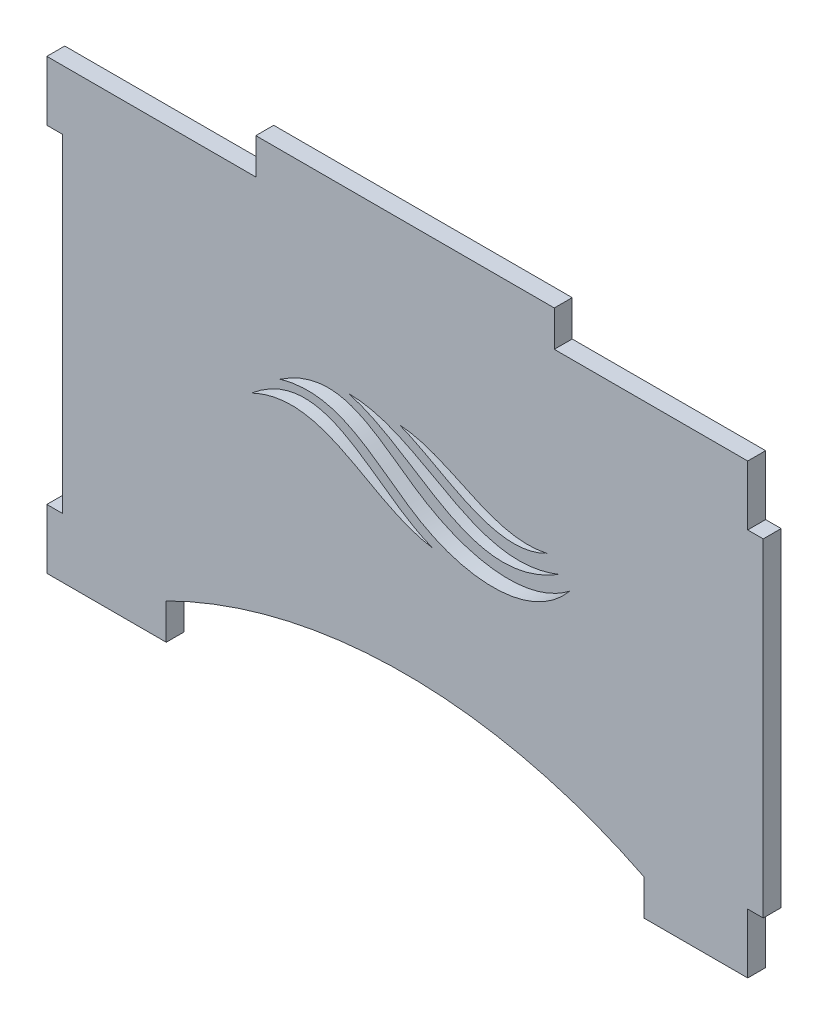
SolidWorks part; units mm, degrees
ref_plane "Front Plane" through (0, 0, 0) normal (0, 0, 1) x (1, 0, 0)
ref_plane "Top Plane" through (0, 0, 0) normal (0, 1, 0) x (1, 0, 0)
ref_plane "Right Plane" through (0, 0, 0) normal (1, 0, 0) x (0, 0, -1)
sketch "Sketch1" plane through (0, 0, 0) normal (0, 0, 1) x (1, 0, 0)
  line L0 (-58.7, -75) -> (-38.7, -75)
  line L3 (-58.7, 0) -> (58.7, 0) construction
  line L5 (58.7, 0) -> (58.7, -10)
  line L6 (58.7, -10) -> (61.3, -10)
  line L7 (58.7, -75) -> (41.3, -75)
  line L8 (61.3, -10) -> (61.3, -65)
  line L9 (61.3, -65) -> (58.7, -65)
  line L10 (58.7, -65) -> (58.7, -75)
  line L11 (-58.7, -75) -> (-58.7, -65)
  line L12 (-58.7, -65) -> (-56.1, -65)
  line L13 (-56.1, -65) -> (-56.1, -10)
  line L14 (-56.1, -10) -> (-58.7, -10)
  line L15 (-58.7, -10) -> (-58.7, 0)
  line L16 (-23.7, 6) -> (26.3, 6)
  line L17 (26.3, 6) -> (26.3, 0)
  line L18 (26.3, 0) -> (58.7, 0)
  line L19 (-23.7, 6) -> (-23.7, 0)
  line L20 (-23.7, 0) -> (-58.7, 0)
  line L21 (41.3, -75) -> (41.3, -69)
  line L22 (41.3, -69) -> (-38.7, -69)
  line L23 (-38.7, -69) -> (-38.7, -75)
  point P0 (0, 0)
  dimension "D1" = 20
  dimension "D3" = 2.6
  dimension "D2" = 120
  dimension "D4" = 20
  dimension "D5" = 6
  dimension "D6" = 50
  dimension "D7" = 10
  dimension "D8" = 75
  dimension "D9" = 6
extrude "Boss-Extrude1" add sketch "Sketch1" along normal blind 3 contours L7 L21 L22 L23 L0 L11 L12 L13 L14 L15 L20 L19 L16 L17 L18 L5 L6 L8 L9 L10
sketch "Sketch2" plane through (0, 0, 0) normal (0, 0, -1) x (-1, 0, 0)
  spline S0 degree 3 poles (24.4334, -31.7116) (12.0869, -21.3752) (4.1402, -35.3582) (-5.9728, -39.0225) knots 0 0 0 0 1 1 1 1
  spline S1 degree 3 poles (24.4334, -31.7116) (12.2668, -25.8916) (4.7867, -37.5421) (-5.9728, -39.0225) knots 0 0 0 0 1 1 1 1
  spline S2 degree 3 poles (19.6339, -27.3096) (8.7369, -24.1379) (-2.1411, -40.4781) (-22.7929, -41.1922) (-28.8934, -33.7725) knots 0 0 0 0 0.516039 1 1 1 1
  spline S3 degree 3 poles (19.6339, -27.3096) (9.0234, -20.1868) (-2.4042, -35.7492) (-21.9217, -39.1582) (-28.8934, -33.7725) knots 0 0 0 0 0.521405 1 1 1 1
  spline S4 degree 3 poles (8.1698, -23.626) (-3.7885, -26.9187) (-12.4208, -41.2866) (-27.1251, -32.2465) knots 0 0 0 0 1 1 1 1
  spline S5 degree 3 poles (8.1698, -23.626) (-4.8002, -23.7533) (-12.7202, -38.0151) (-27.1251, -32.2465) knots 0 0 0 0 1 1 1 1
  spline S6 degree 3 poles (-0.3748, -23.9123) (-7.802, -26.7598) (-16.4033, -34.7893) (-25.1259, -30.1784) knots 0 0 0 0 1 1 1 1
  spline S7 degree 3 poles (-0.3748, -23.9123) (-9.1802, -24.4868) (-15.7739, -32.3988) (-25.1259, -30.1784) knots 0 0 0 0 1 1 1 1
extrude "Cut-Extrude1" cut sketch "Sketch2" against normal through all
sketch "Sketch3" [suppressed] plane through (0, 0, 0) normal (0, 0, -1) x (-1, 0, 0)
  line L0 (23.7, 6) -> (-26.3, 6) construction
  line L1 (-24.8, 6) -> (-27.8, 6)
  line L2 (-24.8, 6) -> (-24.8, -30)
  line L3 (-24.8, -30) -> (-27.8, -30)
  line L4 (-27.8, 6) -> (-27.8, -30)
  line L5 (-26.3, 0) -> (-58.7, 0) construction
  line L6 (22.2, 6) -> (25.2, 6)
  line L7 (22.2, 6) -> (22.2, -30)
  line L8 (22.2, -30) -> (25.2, -30)
  line L9 (25.2, 6) -> (25.2, -30)
  line L10 (-26.3, 6) -> (-26.3, 0) construction
  line L11 (23.7, 6) -> (23.7, 0) construction
  point P10 (-26.3, 6)
  point P13 (23.7, 6)
  dimension "D1" = 3
  dimension "D2" = 30
extrude "Cut-Extrude2" [suppressed] cut sketch "Sketch3" against normal through all
sketch "Sketch4" plane through (0, 0, 0) normal (0, 0, -1) x (-1, 0, 0)
  line L0 (-41.3, -69) -> (38.7, -69) construction
  line L1 (-41.3, -69) -> (38.7, -69)
  arc A0 (-41.3, -69) -> (38.7, -69) centre (-1.3, -149) cw
  point P3 (-1.3, -59.5573)
  point P8 (-1.3, -69)
  dimension "D1" = 80
extrude "Cut-Extrude3" cut sketch "Sketch4" against normal through all contours A0 L1
